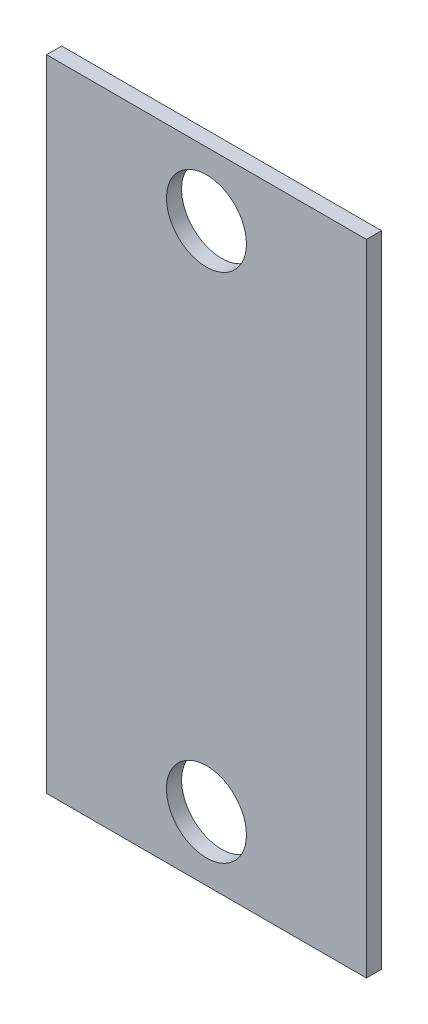
SolidWorks part; units mm, degrees
ref_plane "Front Plane" through (0, 0, 0) normal (0, 0, 1) x (1, 0, 0)
ref_plane "Top Plane" through (0, 0, 0) normal (0, 1, 0) x (1, 0, 0)
ref_plane "Right Plane" through (0, 0, 0) normal (1, 0, 0) x (0, 0, -1)
sketch "Sketch1" plane through (0, 0, 0) normal (0, 0, 1) x (1, 0, 0)
  line L0 (31.75, 0) -> (31.75, -127) construction
  line L1 (0, 0) -> (63.5, 0)
  line L2 (0, 0) -> (0, -127)
  line L3 (0, -127) -> (63.5, -127)
  line L4 (63.5, 0) -> (63.5, -127)
  line L5 (0, -63.5) -> (63.5, -63.5) construction
  circle A0 centre (31.75, -114.3) radius 7.9375
  circle A1 centre (31.75, -12.7) radius 7.9375
  dimension "D3" = 15.875
  dimension "D4" = 15.875
  dimension "D1" = 63.5
  dimension "D2" = 127
  dimension "D5" = 12.7
  dimension "D6" = 12.7
extrude "Boss-Extrude2" add sketch "Sketch1" along normal blind 2.9972
